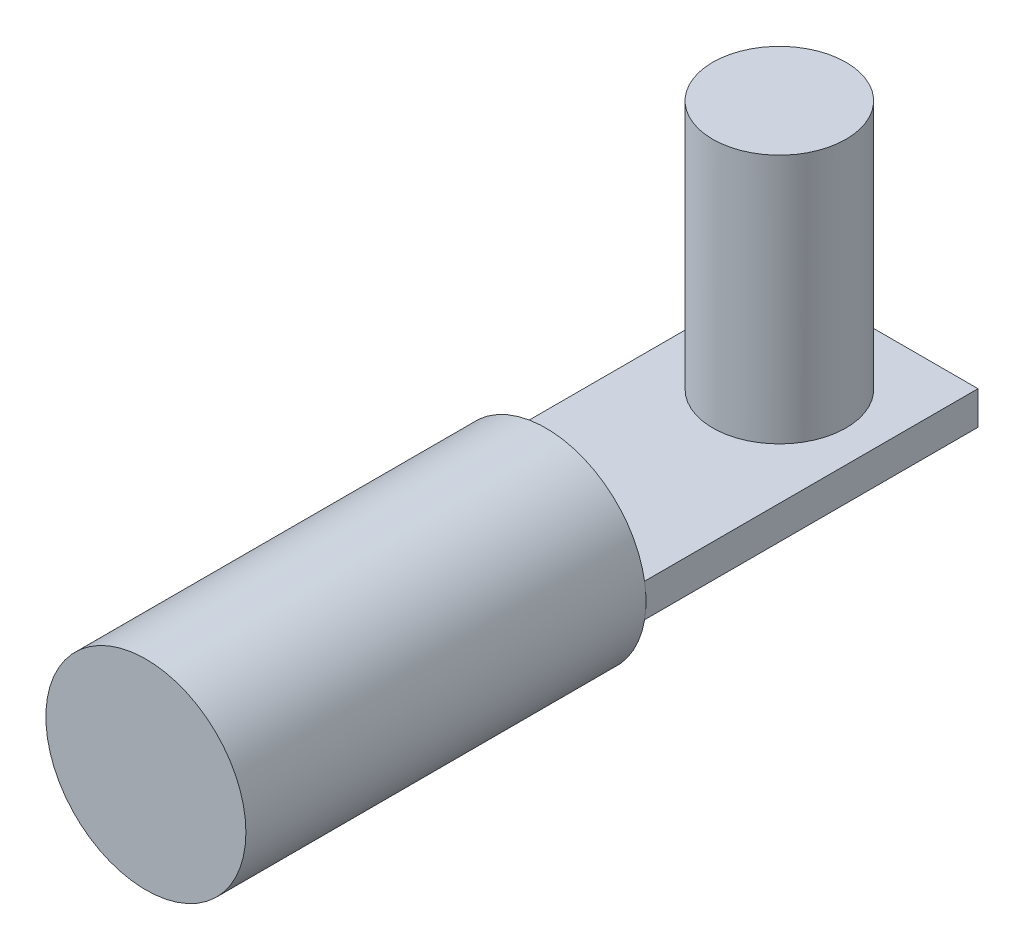
SolidWorks part; units mm, degrees
ref_plane "Front Plane" through (0, 0, 0) normal (0, 0, 1) x (1, 0, 0)
ref_plane "Top Plane" through (0, 0, 0) normal (0, 1, 0) x (1, 0, 0)
ref_plane "Right Plane" through (0, 0, 0) normal (1, 0, 0) x (0, 0, -1)
sketch "Sketch1" plane through (0, 0, 0) normal (0, 0, 1) x (1, 0, 0)
  circle A0 centre (0, 0) radius 3
  dimension "D1" = 6
extrude "Boss-Extrude1" add sketch "Sketch1" along normal blind 12
sketch "Sketch2" plane through (0, 0, 0) normal (0, 0, -1) x (-1, 0, 0)
  line L9 (-2.9578, -0.5013) -> (2.9578, -0.5013)
  line L10 (-2.9578, -0.5013) -> (-2.9578, 0.5013)
  line L11 (-2.9578, 0.5013) -> (2.9578, 0.5013)
  line L12 (2.9578, -0.5013) -> (2.9578, 0.5013)
  line L13 (-2.9578, -0.5013) -> (2.9578, 0.5013) construction
  line L14 (-2.9578, 0.5013) -> (2.9578, -0.5013) construction
  circle A1 centre (0, 0) radius 3 construction
  point P0 (0, 0)
extrude "Boss-Extrude2" add sketch "Sketch2" along normal blind 10
sketch "Sketch4" plane through (0, 0.5013, 0) normal (0, 1, 0) x (1, 0, 0)
  line L0 (0, 10) -> (0, 7) construction
  line L1 (-2.9578, 10) -> (2.9578, 10) construction
  circle A0 centre (0, 7) radius 2
  dimension "D2" = 4
  dimension "D1" = 3
extrude "Boss-Extrude3" add sketch "Sketch4" along normal blind 7.5
